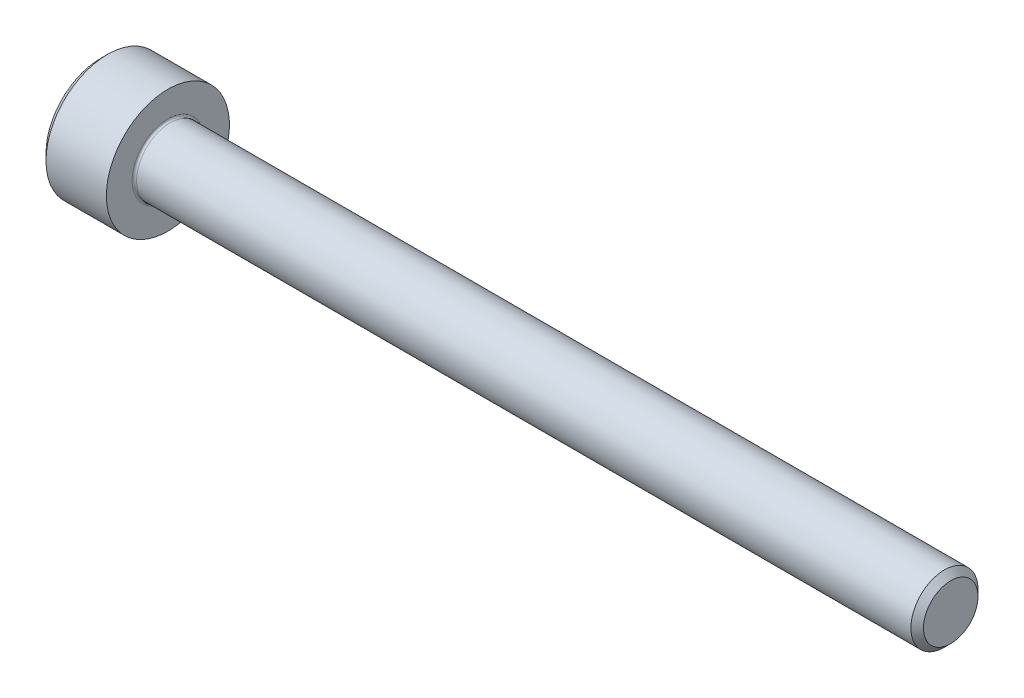
SolidWorks part; units mm, degrees
revolve "Base-Revolve" add sketch "BodySke"
sketch "BodySke" plane through (0, 0, 0) normal (0, 0, 1) x (1, 0, 0)
  line L0 (0, 0) -> (0, 2.45)
  line L1 (0.3, 2.75) -> (3, 2.75)
  line L2 (3, 2.75) -> (3, 1.5)
  line L3 (3, 1.5) -> (37.7195, 1.5)
  line L4 (38, 1.2195) -> (38, 0)
  line L5 (38, 0) -> (0, 0)
  line L6 (-31.75, 0) -> (127, 0) construction
  line L7 (0, 2.45) -> (0.3, 2.75)
  line L8 (38, 1.2195) -> (37.7195, 1.5)
  line L9 (0, -2.45) -> (0.3, -2.75) construction
  line L10 (38, -1.2195) -> (37.7195, -1.5) construction
  line L11 (3.5, 9.525) -> (3.5, 3.175) construction
  line L12 (20, 9.525) -> (20, 3.175) construction
  line L13 (-12, 9.525) -> (-12, 3.175) construction
  dimension "Diameter" = 3
  dimension "Head_ht" = 3
  dimension "Length" = 35
  dimension "Body_ch_ang" = 45
  dimension "Head_dia" = 5.5
  dimension "Head_ch_ang" = 45
  dimension "Minor_dia" = 2.439
  dimension "Advance" = 0.5
  dimension "Thread_nom" = 18
  dimension "Thread_length" = 50
  dimension "Head_ch_ht" = 0.3
cosmetic thread "ThreadCosmetic"
fillet "Fillet1" radius 0.1 1 edges at (3, 0, 1.5)
ref_plane "Plane1" through (0, 0, 0) normal (0, 0, 1) x (1, 0, 0)
ref_plane "Plane2" through (0, 0, 0) normal (0, 1, 0) x (1, 0, 0)
ref_plane "Plane3" through (0, 0, 0) normal (1, 0, 0) x (0, 0, -1)
sketch "Sketch2" plane through (0, 0, 0) normal (0, 0, 1) x (1, 0, 0)
  line L0 (0, 1.28) -> (1.3, 1.28)
  line L1 (1.3, 1.28) -> (2.039, 0)
  line L2 (-31.75, 0) -> (127, 0) construction
  line L3 (2.039, 0) -> (0, 0)
  line L4 (0, 0) -> (0, 1.28)
  line L5 (0, 2.45) -> (0, -2.45) construction
  line L6 (0, 0) -> (47.625, 0) construction
  line L7 (3, -2.75) -> (3, 2.75) construction
  dimension "D1" = 1.28
  dimension "D2" = 60
revolve "Hex-PreBroach" cut sketch "Sketch2" angle 360 about L6
sketch "Sketch3" plane through (0, 0, 0) normal (-1, 0, 0) x (0, 0.5, 0.866)
  line L0 (0.739, 1.28) -> (-0.739, 1.28)
  line L1 (-0.739, 1.28) -> (-1.478, 0)
  line L2 (0.739, 1.28) -> (1.478, 0)
  line L3 (0.739, -1.28) -> (1.478, 0)
  line L4 (0.739, -1.28) -> (-0.739, -1.28)
  line L5 (-0.739, -1.28) -> (-1.478, 0)
  dimension "D1" = 1.28
  dimension "D2" = 1.28
  dimension "Hex_size" = 2.56
extrude "Hex" cut sketch "Sketch3" against normal blind 1.3
sketch "Sketch4" plane through (0, 0, 0) normal (-1, 0, 0) x (0, 0, 1)
  line L0 (0, 0) -> (1.4605, 0)
  line L1 (0, 0) -> (6.1484, 3.5498) construction
  line L2 (0, 0) -> (0.7302, 1.2648)
  line L3 (1.2009, 0.3267) -> (1.3933, 0.4378)
  line L4 (0.8834, 0.8767) -> (1.0758, 0.9877)
  arc A0 (1.2009, 0.3267) -> (0.8834, 0.8767) centre (0, 0) ccw
  arc A1 (1.4605, 0) -> (1.3933, 0.4378) centre (0, 0) ccw
  arc A2 (0.7302, 1.2648) -> (1.0758, 0.9877) centre (0, 0) cw
  dimension "D1" = 30
  dimension "D2" = 60
  dimension "Spline_p_dim" = 0.635
  dimension "D3" = 0.3175
extrude "Spline" [suppressed] cut sketch "Sketch4" against normal blind 1.3
pattern_circular "CirPattern1" [suppressed] count 6 every 60
sketch "Sketch5" plane through (0, 0, 0) normal (0, 0, 1) x (1, 0, 0)
  line L0 (-31.75, 0) -> (127, 0) construction
  line L2 (0, 2.45) -> (0, -2.45) construction
  circle A0 centre (1.2, 0) radius 0.475
  dimension "Drilled_hole_dia" = 0.95
  dimension "Drilled_hole_loc" = 1.2
extrude "Hole" [suppressed] cut sketch "Sketch5" against normal through all and the other way through all
pattern_circular "Drilled-4" [suppressed] count 2 every 60
pattern_circular "Drilled-6" [suppressed] count 3 every 60
sketch "ThdSchSke" plane through (0, 0, 0) normal (0, 0, 1) x (1, 0, 0)
  line L0 (20, -1.2195) -> (19.8036, -1.5)
  line L1 (20, -1.2195) -> (20.1964, -1.5)
  line L2 (20.1964, -1.5) -> (20.1964, -1.875)
  line L3 (-3.175, 0) -> (5.1513, 0) construction
  line L5 (20.1964, -1.875) -> (19.8036, -1.875)
  line L6 (19.8036, -1.875) -> (19.8036, -1.5)
  line L7 (0, 2.45) -> (0, -2.45) construction
  dimension "Thread_minor" = 2.439
  dimension "Diameter" = 3
  dimension "Start" = 20
revolve "ThreadSchematic" [suppressed] cut sketch "ThdSchSke" angle 360 about L3
pattern_linear "ThdSchPat" [suppressed]
equation "\"D2@Sketch3\" = \"Hex_size@Sketch3\" / 2"
equation "\"D1@Sketch3\" = \"Hex_size@Sketch3\" / 2"
equation "\"D1@Sketch2\" = \"Hex_size@Sketch3\" / 2"
equation "\"D3@Sketch4\" = \"Spline_p_dim@Sketch4\" / 2"
equation "\"Thread_minor@ThreadCosmetic\"  =  \"Minor_dia@BodySke\""
equation "\"D2@CirPattern1\" = 360 / \"Num_teeth@CirPattern1\""
equation "\"Wall_thickness@Sketch2\" = \"Head_ht@BodySke\" - \"Key_eng@Hex\""
equation "\"Thread_length@ThreadCosmetic\" = ((sgn( (\"Length@BodySke\" - \"Advance@BodySke\" ) - \"Thread_nom@BodySke\" )-1)*( (\"Length@BodySke\" - \"Advance@BodySke\" ) - \"Thread_nom@BodySke\" ))/-2+ \"Thread_nom@BodySke\""
equation "\"Thread_minor@ThdSchSke\" = \"Minor_dia@BodySke\""
equation "\"Diameter@ThdSchSke\" = \"Diameter@BodySke\""
equation "\"Overcut@ThdSchSke\" = \"Diameter@BodySke\" * 1.25"
equation "\"Start@ThdSchSke\" = \"Head_ht@BodySke\" + \"Length@BodySke\" - \"Thread_length@ThreadCosmetic\"  '---Non-countersunk---"
equation "\"Num_threads@ThdSchPat\" = int( \"Thread_length@ThreadCosmetic\" / \"Advance@BodySke\" + 0.999 )  + 1"
equation "\"Advance@ThdSchPat\" = \"Thread_length@ThreadCosmetic\" /  (\"Num_threads@ThdSchPat\" - 1) 'relax it"
equation "\"Num_threads@ThdSchPat\" = \"Num_threads@ThdSchPat\" - sgn( \"Num_threads@ThdSchPat\" - 1) '---chamfered tips only---"
